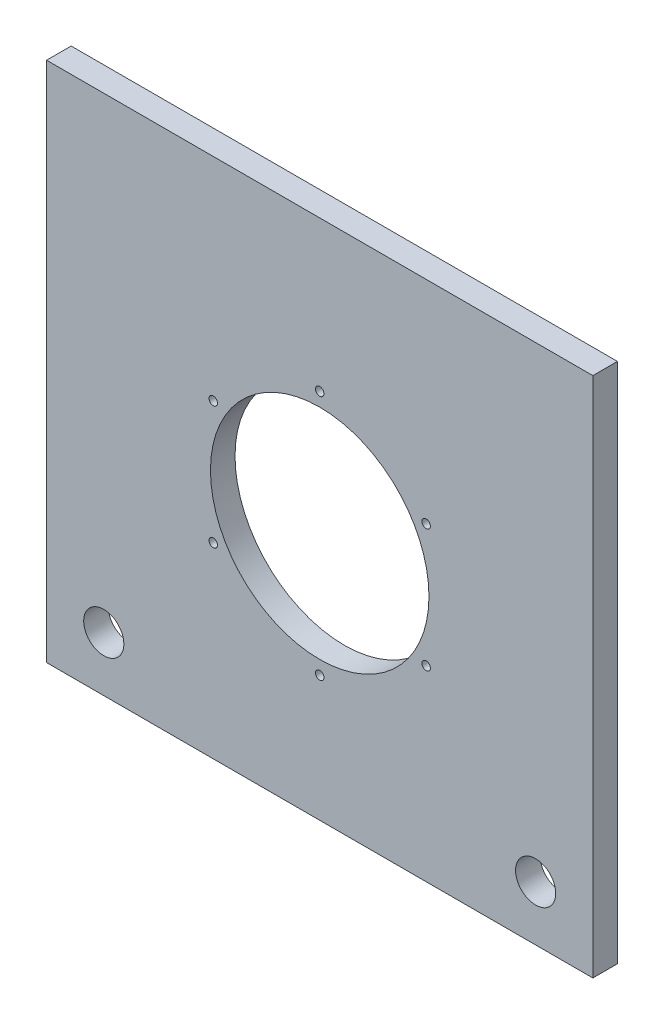
SolidWorks part; units mm, degrees
ref_plane "前视基准面" through (0, 0, 0) normal (0, 0, 1) x (1, 0, 0)
ref_plane "上视基准面" through (0, 0, 0) normal (0, 1, 0) x (1, 0, 0)
ref_plane "右视基准面" through (0, 0, 0) normal (1, 0, 0) x (0, 0, -1)
other "Configuration Table"
sketch "草图1" plane through (0, 0, 0) normal (0, 0, 1) x (1, 0, 0)
  line L0 (0, -1000) -> (0, 49000) construction
  line L1 (-100, 95.5) -> (100, 95.5)
  line L2 (-100, 95.5) -> (-100, -95.5)
  line L3 (-100, -95.5) -> (100, -95.5)
  line L4 (100, 95.5) -> (100, -95.5)
  line L5 (-100, 95.5) -> (100, -95.5) construction
  line L6 (-100, -95.5) -> (100, 95.5) construction
  circle A0 centre (0, -4.5) radius 40
  circle A1 centre (-79.0576, -75.5) radius 7.35
  circle A2 centre (79.0576, -75.5) radius 7.35
  circle A3 centre (0, -4.5) radius 45 construction
  circle A4 centre (0, 40.5) radius 1.55
  circle A5 centre (38.9711, 18) radius 1.55
  circle A6 centre (38.9711, -27) radius 1.55
  circle A7 centre (0, -49.5) radius 1.55
  circle A8 centre (-38.9711, -27) radius 1.55
  circle A9 centre (-38.9711, 18) radius 1.55
  point P0 (0, 0)
  point P18 (48.572, 18.2739)
  point P19 (0, 0)
  point P31 (0, -4.5)
  dimension "D4" = 80
  dimension "D5" = 14.7
  dimension "D8" = 3.1
  dimension "D1" = 200
  dimension "D2" = 191
  dimension "D3" = 91
  dimension "D6" = 20
  dimension "D7" = 5
  dimension "D9" = 6
extrude "凸台-拉伸1" add sketch "草图1" along normal blind 9
